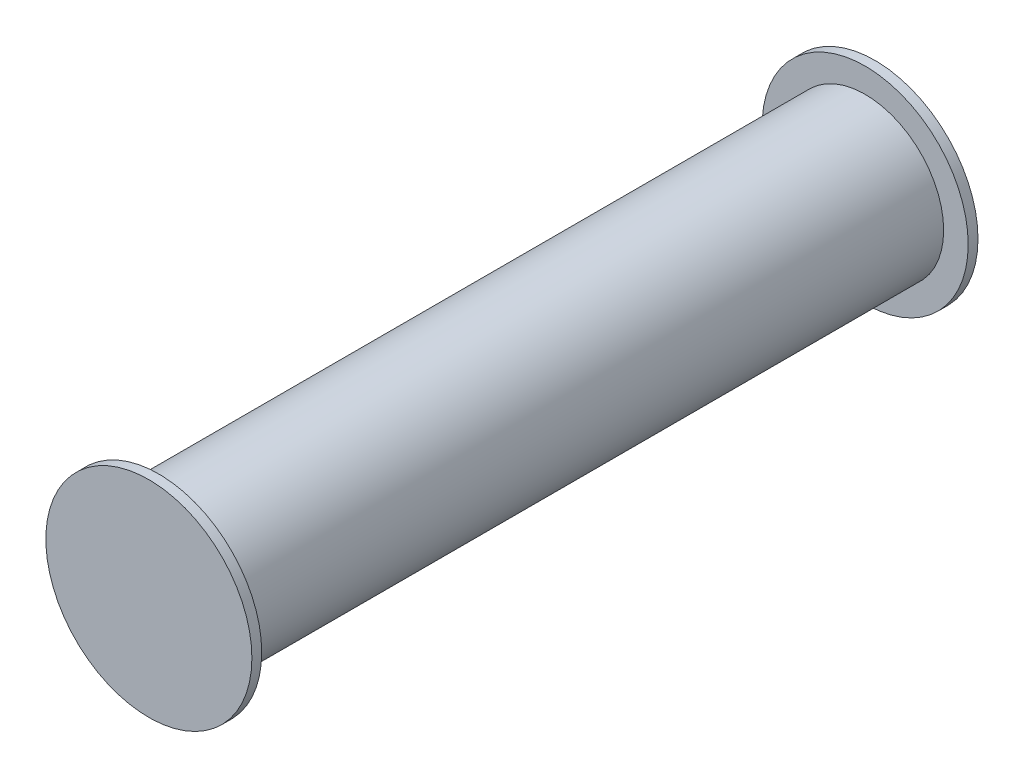
SolidWorks part; units mm, degrees
material "6061 Alloy"
ref_plane "Front Plane" through (0, 0, 0) normal (0, 0, 1) x (1, 0, 0)
ref_plane "Top Plane" through (0, 0, 0) normal (0, 1, 0) x (1, 0, 0)
ref_plane "Right Plane" through (0, 0, 0) normal (1, 0, 0) x (0, 0, -1)
sketch "Sketch1" plane through (0, 0, 0) normal (0, 0, 1) x (1, 0, 0)
  circle A0 centre (0, 0) radius 50.8
  dimension "D1" = 101.6
extrude "Boss-Extrude1" add sketch "Sketch1" along normal blind 457.2
sketch "Sketch2" plane through (0, 0, 457.2) normal (0, 0, 1) x (1, 0, 0)
  circle A0 centre (0, 0) radius 41.275
  dimension "D1" = 82.55
extrude "Cut-Extrude1" cut sketch "Sketch2" against normal blind 457.2
sketch "Sketch3" plane through (0, 0, 457.2) normal (0, 0, 1) x (1, 0, 0)
  circle A0 centre (0, 0) radius 66.675
  dimension "D1" = 133.35
extrude "Boss-Extrude2" add sketch "Sketch3" along normal blind 6.35
ref_plane "Plane1" through (0, 0, 228.6) normal (0, 0, 1) x (1, 0, 0)
mirror "Mirror1" about plane through (0, 0, 228.6) normal (0, 0, 1) of "Boss-Extrude2"
